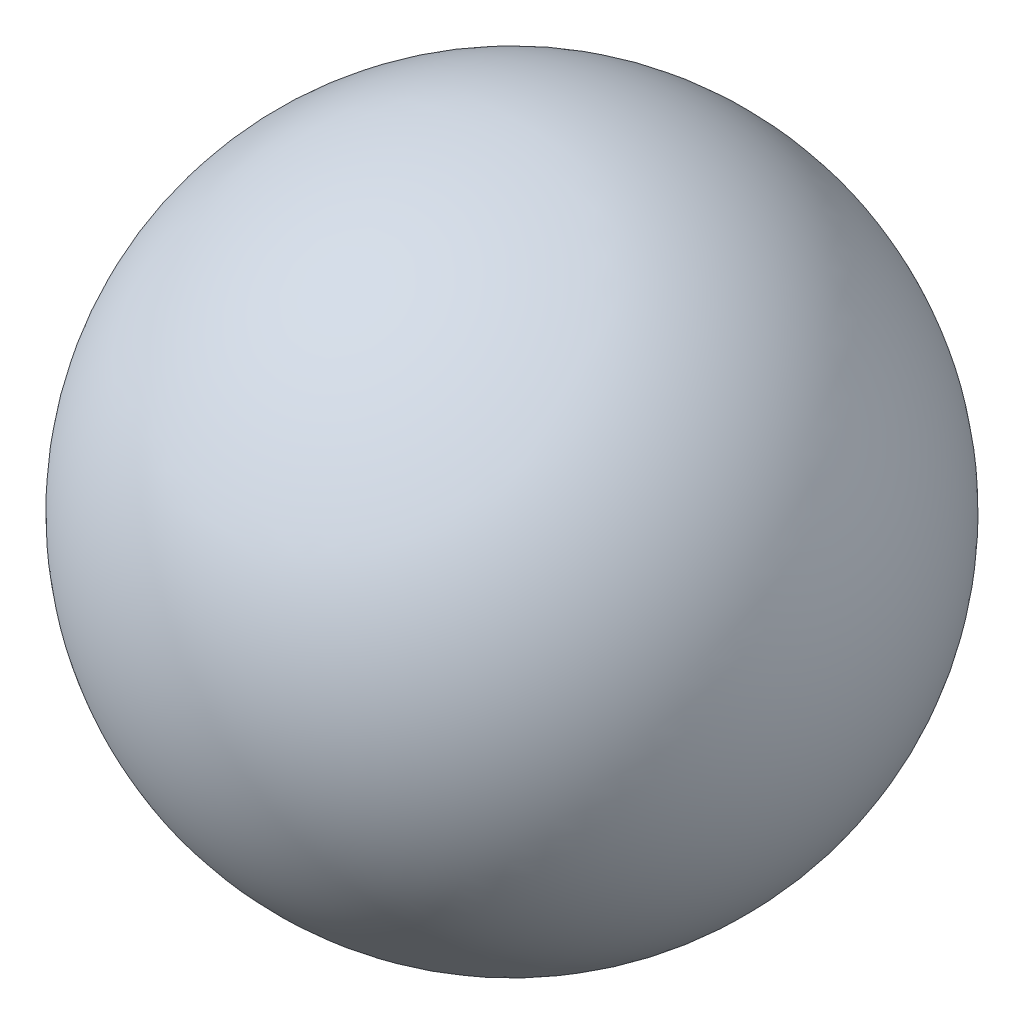
SolidWorks part; units mm, degrees
material "Rubber"
ref_plane "Front Plane" through (0, 0, 0) normal (0, 0, 1) x (1, 0, 0)
ref_plane "Top Plane" through (0, 0, 0) normal (0, 1, 0) x (1, 0, 0)
ref_plane "Right Plane" through (0, 0, 0) normal (1, 0, 0) x (0, 0, -1)
sketch "Sketch1" plane through (0, 0, 0) normal (0, 1, 0) x (1, 0, 0)
  line L0 (0, 20) -> (0, -20)
  arc A0 (0, 20) -> (0, -20) centre (0, 0) ccw
  dimension "D1" = 40
revolve "Revolve1" add sketch "Sketch1" angle 360 about L0
